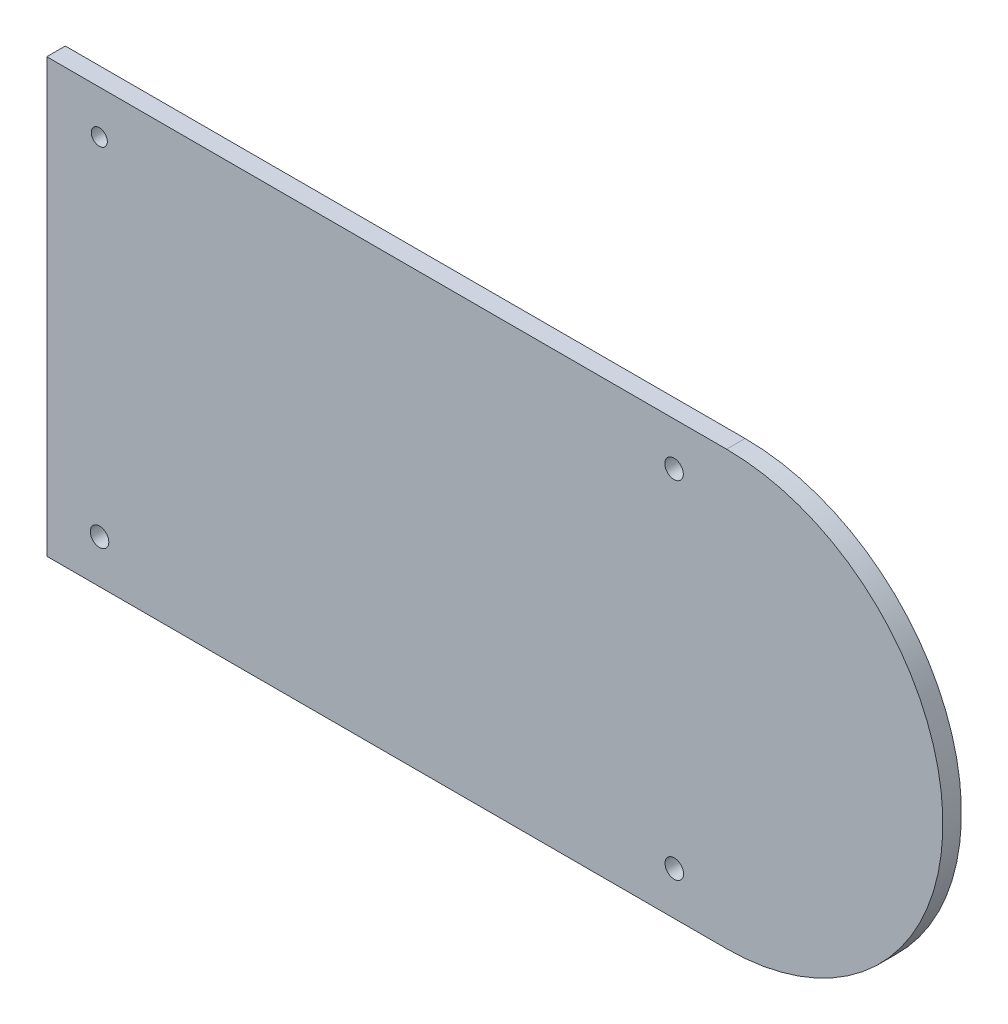
SolidWorks part; units mm, degrees
ref_plane "Front Plane" through (0, 0, 0) normal (0, 0, 1) x (1, 0, 0)
ref_plane "Top Plane" through (0, 0, 0) normal (0, 1, 0) x (1, 0, 0)
ref_plane "Right Plane" through (0, 0, 0) normal (1, 0, 0) x (0, 0, -1)
sketch "Sketch1" plane through (0, 0, 0) normal (0, 0, 1) x (1, 0, 0)
  line L0 (-67.4317, 21.979) -> (-67.4317, -48.021)
  line L1 (-67.4317, -48.021) -> (42.5683, -48.021)
  line L3 (42.5683, 21.979) -> (-67.4317, 21.979)
  arc A0 (42.5683, 21.979) -> (42.5683, -48.021) centre (42.5683, -13.021) cw
  circle A1 centre (-58.9317, 14.979) radius 1.3
  circle A2 centre (34.0683, 14.979) radius 1.5
  circle A3 centre (34.1049, -41.021) radius 1.5
  circle A4 centre (-58.8951, -41.021) radius 1.5
extrude "Boss-Extrude1" add sketch "Sketch1" along normal blind 3
